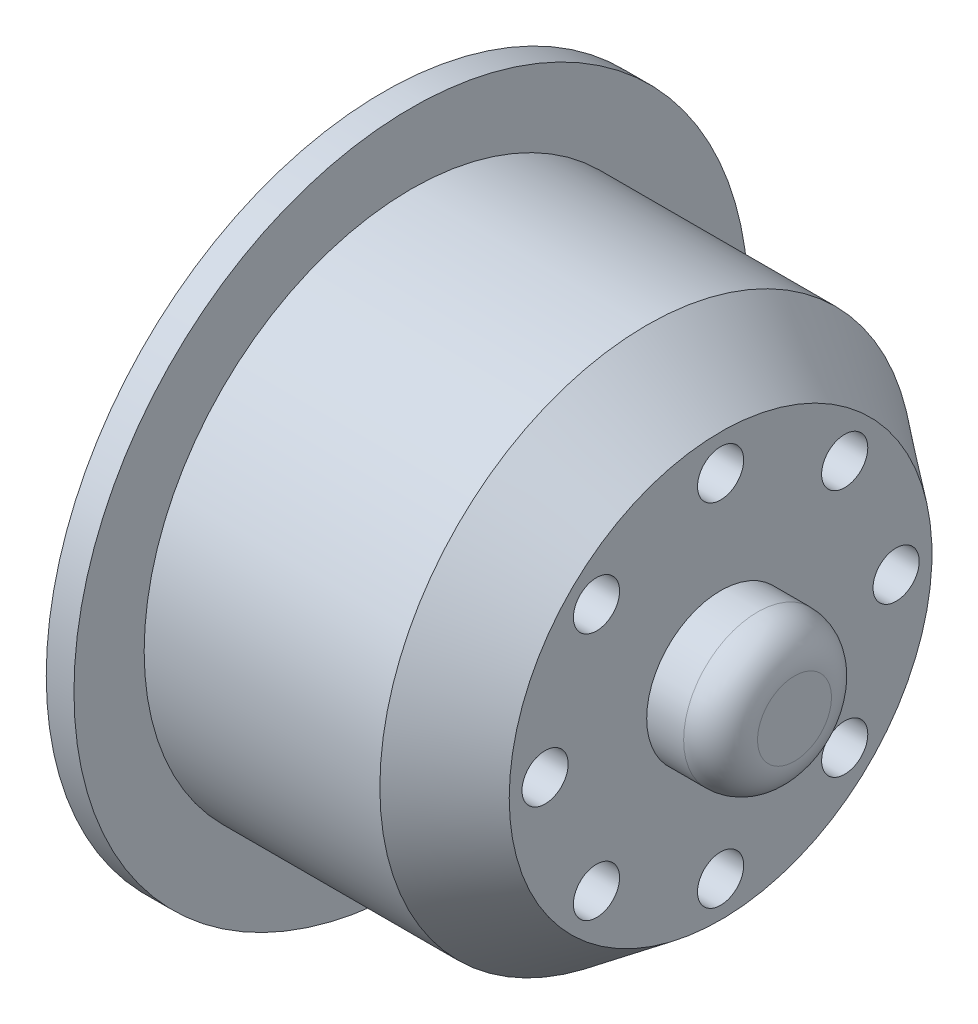
SolidWorks part; units mm, degrees
ref_plane "Front Plane" through (0, 0, 0) normal (0, 0, 1) x (1, 0, 0)
ref_plane "Top Plane" through (0, 0, 0) normal (0, 1, 0) x (1, 0, 0)
ref_plane "Right Plane" through (0, 0, 0) normal (1, 0, 0) x (0, 0, -1)
sketch "Sketch1" plane through (0, 0, 0) normal (0, 1, 0) x (1, 0, 0)
  line L0 (-12.3913, 0) -> (21, 0) construction
  line L1 (-6.1304, 14.45) -> (6.6264, 14.45)
  line L2 (6.6264, 14.45) -> (10.6196, 11.4409)
  line L5 (13.3727, 0) -> (-6.1304, 0)
  line L7 (10.6196, 11.4409) -> (10.6196, 4)
  line L8 (10.6196, 4) -> (14.6196, 4)
  line L9 (14.6196, 4) -> (14.6196, 0)
  line L10 (14.6196, 0) -> (13.3727, 0)
  line L11 (-6.1304, 14.45) -> (-6.1304, 18.25)
  line L12 (-6.1304, 18.25) -> (-7.6304, 18.25)
  line L13 (-7.6304, 18.25) -> (-7.6304, 0)
  line L14 (-7.6304, 0) -> (-6.1304, 0)
  dimension "D1" = 3.9932
  dimension "D2" = 143
  dimension "D3" = 127
  dimension "D4" = 5
  dimension "D5" = 28.9
  dimension "D6" = 16.75
  dimension "D7" = 4
  dimension "D8" = 8
  dimension "D9" = 3.8
  dimension "D10" = 1.5
revolve "Revolve1" add sketch "Sketch1" angle 360 about L0
sketch "Sketch2" plane through (10.6196, 0, 0) normal (1, 0, 0) x (0, 0, -1)
  circle A0 centre (0, 0) radius 9.5 construction
  circle A1 centre (0, 9.5) radius 1.25
  circle A3 centre (6.7175, 6.7175) radius 1.25
  circle A4 centre (9.5, 0) radius 1.25
  circle A5 centre (6.7175, -6.7175) radius 1.25
  circle A6 centre (0, -9.5) radius 1.25
  circle A7 centre (-6.7175, -6.7175) radius 1.25
  circle A8 centre (-9.5, 0) radius 1.25
  circle A9 centre (-6.7175, 6.7175) radius 1.25
  point P22 (0, 0)
  dimension "D1" = 19
  dimension "D2" = 2.5
  dimension "D3" = 8
extrude "Cut-Extrude1" cut sketch "Sketch2" against normal through all
fillet "Fillet1" radius 2 1 edges at (14.6196, 0, 4)
sketch "Sketch3" plane through (-7.6304, 0, 0) normal (-1, 0, 0) x (0, 0, 1)
  circle A0 centre (0, 0) radius 9.5 construction
  circle A1 centre (0, 9.5) radius 2.5
  circle A2 centre (6.7175, 6.7175) radius 2.5
  circle A3 centre (9.5, 0) radius 2.5
  circle A4 centre (6.7175, -6.7175) radius 2.5
  circle A5 centre (0, -9.5) radius 2.5
  circle A6 centre (-6.7175, -6.7175) radius 2.5
  circle A7 centre (-9.5, 0) radius 2.5
  circle A8 centre (-6.7175, 6.7175) radius 2.5
  point P23 (0, 0)
  dimension "D1" = 19
  dimension "D2" = 5
  dimension "D3" = 8
extrude "Cut-Extrude2" cut sketch "Sketch3" against normal offset from surface (13.25 mm away) 5 up to face at (10.6196, 9.5, -1.25)
sketch "Sketch4" plane through (-7.6304, 0, 0) normal (-1, 0, 0) x (0, 0, 1)
  circle A0 centre (0, 0) radius 11
  dimension "D1" = 22
extrude "Cut-Extrude3" cut sketch "Sketch4" against normal blind 6
